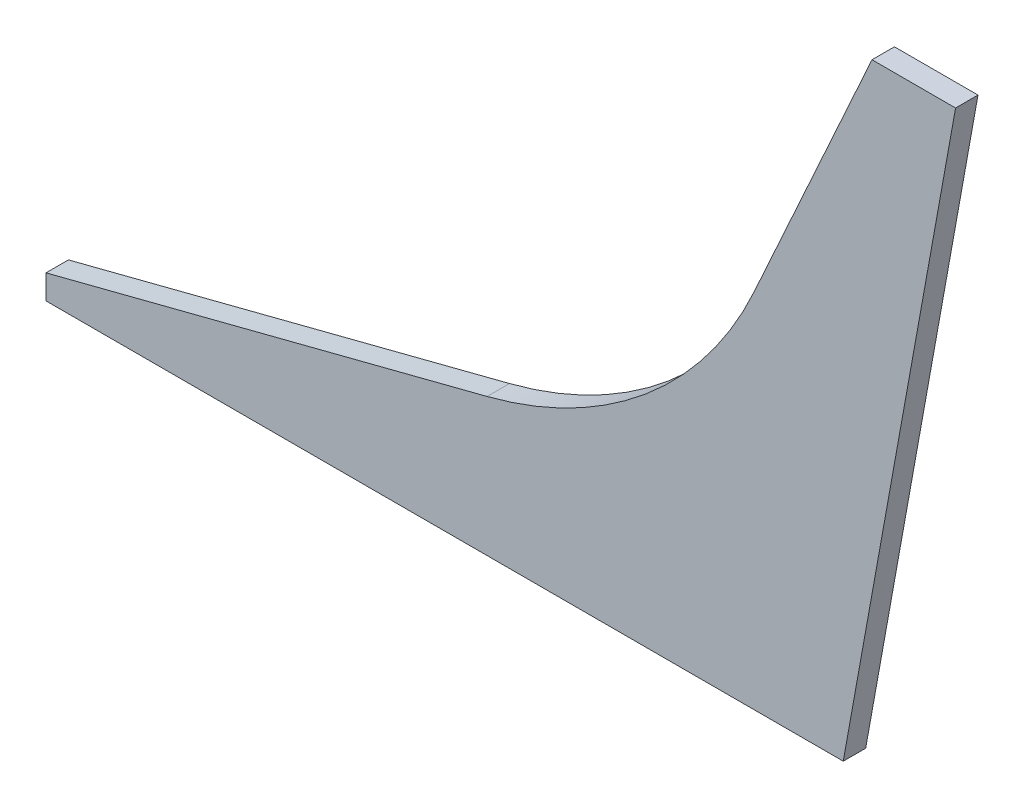
SolidWorks part; units mm, degrees
ref_plane "Front Plane" through (0, 0, 0) normal (0, 0, 1) x (1, 0, 0)
ref_plane "Top Plane" through (0, 0, 0) normal (0, 1, 0) x (1, 0, 0)
ref_plane "Right Plane" through (0, 0, 0) normal (1, 0, 0) x (0, 0, -1)
sketch "Sketch1" plane through (0, 0, 0) normal (0, 0, 1) x (1, 0, 0)
  line L0 (-236.7294, 0) -> (236.7294, 0) construction
  line L1 (-236.7294, 0) -> (0, 0)
  line L2 (0, 0) -> (357.8768, 0)
  line L3 (357.8768, 0) -> (396.7304, 416)
  line L4 (396.7304, 416) -> (315.8328, 416)
  line L5 (315.8328, 416) -> (236.9831, 242.1445)
  line L6 (58.3523, 92.1777) -> (-236.7294, 16.2749)
  line L7 (-236.7294, 16.2749) -> (-236.7294, 0)
  arc A0 (236.9831, 242.1445) -> (58.3523, 92.1777) centre (-8.9093, 353.6655) cw
  point P4 (0, 0)
  point P39 (183.5766, 124.3887)
  dimension "D4" = 270
  dimension "D3" = 416
extrude "Boss-Extrude1" add sketch "Sketch1" along normal blind 15
sketch "Sketch2" plane through (0, 0, 15) normal (0, 0, 1) x (1, 0, 0)
  line L0 (396.7304, 416) -> (357.8768, 0)
  line L1 (357.8768, 0) -> (296.5972, 0)
  line L2 (-236.7294, 0) -> (357.8768, 0) construction
  line L3 (296.5972, 0) -> (371.7349, 416)
  line L4 (396.7304, 416) -> (315.8328, 416) construction
  line L5 (371.7349, 416) -> (396.7304, 416)
  line L6 (329.6881, 183.2077) -> (374.9881, 183.2077) construction
  dimension "D1" = 45.3
extrude "Cut-Extrude1" cut sketch "Sketch2" against normal through all both and the other way through all
